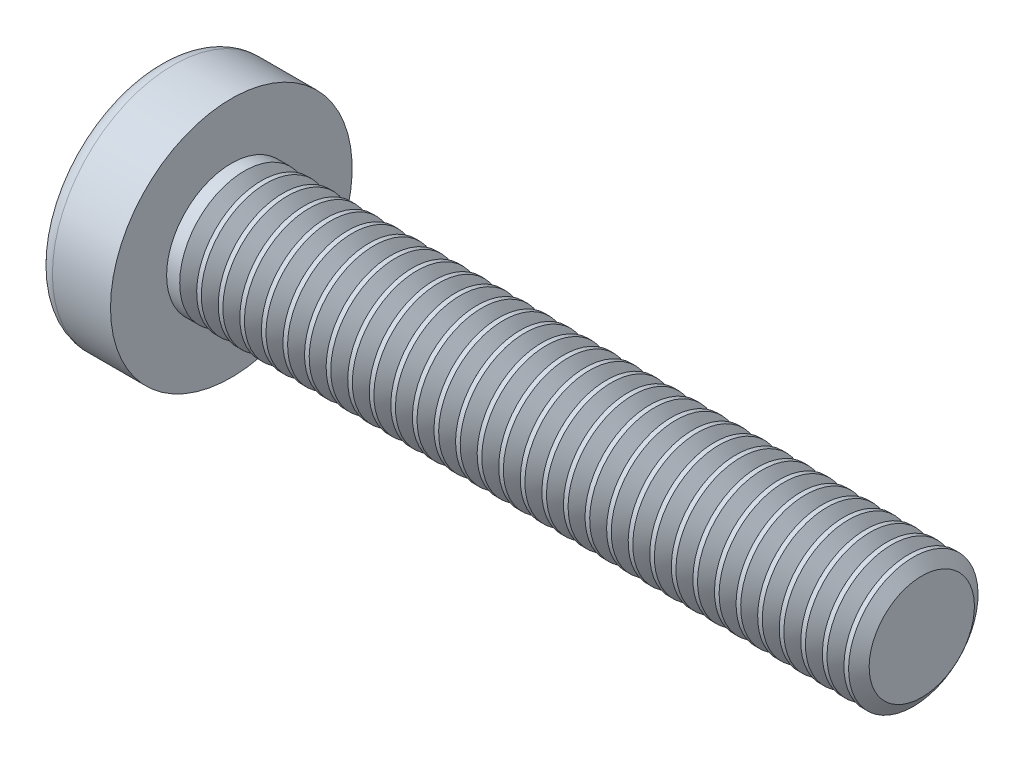
SolidWorks part; units mm, degrees
ref_plane "Plane1" through (0, 0, 0) normal (0, 0, 1) x (1, 0, 0)
ref_plane "Plane2" through (0, 0, 0) normal (0, 1, 0) x (1, 0, 0)
ref_plane "Plane3" through (0, 0, 0) normal (1, 0, 0) x (0, 0, -1)
sketch "BodySke" plane through (0, 0, 0) normal (0, 0, 1) x (1, 0, 0)
  line L0 (2.4, 1.5) -> (2.4, 2.8)
  line L1 (2.9, 6.35) -> (2.9, -3.175) construction
  line L2 (-25.4, 0) -> (127, 0) construction
  line L3 (18.4, 0) -> (0, 0)
  line L4 (2.4, 1.5) -> (18.4, 1.5)
  line L5 (18.4, 1.5) -> (18.4, 0)
  line L6 (1.0534, 2.8) -> (2.4, 2.8)
  line L7 (2.4, -1.5) -> (18.4, -1.5) construction
  line L8 (2.4, 6.35) -> (2.4, -3.175) construction
  arc A0 (0.7472, 2.6293) -> (0, 0) centre (5, 0) ccw
  arc A2 (0.7472, 2.6293) -> (1.0534, 2.8) centre (1.0534, 2.44) cw
  dimension "Head_crown_rad" = 5
  dimension "Head_fillet_rad" = 0.36
  dimension "Diameter" = 3
  dimension "Head_ht" = 2.4
  dimension "Head_dia" = 5.6
  dimension "Advance" = 0.5
revolve "Base-Revolve" add sketch "BodySke" angle 360 about L2
cosmetic thread "ThreadCosmetic" [suppressed] parameters "Thread_length"=15.5, "Thread_minor"=2.439
sketch "Sketch3" plane through (0, 0, 0) normal (1, 0, 0) x (0, 0, -1)
  line L0 (0.37, -1.45) -> (-0.37, -1.45)
  line L1 (0.37, -1.45) -> (0.37, 1.45)
  line L2 (-0.37, 1.45) -> (0.37, 1.45)
  line L3 (-0.37, 1.45) -> (-0.37, -1.45)
  dimension "Cross_dia" = 2.9
  dimension "D1" = 1.45
  dimension "Cross_width" = 0.74
  dimension "D2" = 0.37
ref_plane "Plane4" through (1.76, 0, 0) normal (1, 0, 0) x (0, 0, -1)
sketch "Sketch4" plane through (1.76, 0, 0) normal (1, 0, 0) x (0, 0, -1)
  line L0 (0.185, -0.185) -> (-0.185, -0.185)
  line L1 (0.185, -0.185) -> (0.185, 0.185)
  line L2 (-0.185, 0.185) -> (0.185, 0.185)
  line L3 (-0.185, 0.185) -> (-0.185, -0.185)
  dimension "D2" = 0.37
  dimension "D1" = 0.37
  dimension "D3" = 0.185
  dimension "D4" = 0.185
loft "Cut-Loft1" cut profiles "Sketch3", "Sketch4"
pattern_circular "CirPattern1" count 2 every 90 about axis through (0, 0, 0) along (1, 0, 0) of "Cut-Loft1"
sketch "ThdSchSke" plane through (0, 0, 0) normal (0, 0, 1) x (1, 0, 0)
  line L0 (2.9, -1.2195) -> (2.7036, -1.5)
  line L1 (2.9, -1.2195) -> (3.0964, -1.5)
  line L2 (3.0964, -1.5) -> (3.0964, -1.875)
  line L3 (-3.175, 0) -> (5.1513, 0) construction
  line L5 (3.0964, -1.875) -> (2.7036, -1.875)
  line L6 (2.7036, -1.875) -> (2.7036, -1.5)
  dimension "Diameter" = 3
  dimension "SideAngle" = 55
  dimension "VeeAngle" = 70
  dimension "Thread_minor" = 2.439
  dimension "Overcut" = 3.75
  dimension "Start" = 2.9
revolve "ThreadSchematic" cut sketch "ThdSchSke" angle 360 about L3
pattern_linear "ThdSchPat" count 32 spacing 0.5 along (1, 0, 0) of "ThreadSchematic"
equation "\"D1@Sketch3\" = \"Cross_dia@Sketch3\" / 2"
equation "\"D2@Sketch3\" = \"Cross_width@Sketch3\" / 2"
equation "\"D1@Sketch4\" = \"Cross_width@Sketch3\" *.5"
equation "\"D2@Sketch4\" = \"D1@Sketch4\""
equation "\"D3@Sketch4\" = \"D1@Sketch4\" / 2"
equation "\"D4@Sketch4\" = \"D2@Sketch4\" / 2"
equation "\"Thread_length@ThreadCosmetic\" = ((sgn( (\"Length@BodySke\" - \"Advance@BodySke\" ) - \"Thread_nom@BodySke\" )-1)*( (\"Length@BodySke\" - \"Advance@BodySke\" ) - \"Thread_nom@BodySke\" ))/-2+ \"Thread_nom@BodySke\""
equation "\"Thread_minor@ThdSchSke\" = \"Thread_minor@ThreadCosmetic\""
equation "\"Diameter@ThdSchSke\" = \"Diameter@BodySke\""
equation "\"Overcut@ThdSchSke\" = \"Diameter@BodySke\" * 1.25"
equation "\"Start@ThdSchSke\" = \"Head_ht@BodySke\" + \"Length@BodySke\" - \"Thread_length@ThreadCosmetic\"  '---Non-countersunk---"
equation "\"Num_threads@ThdSchPat\" = int( \"Thread_length@ThreadCosmetic\" / \"Advance@BodySke\" + 0.999 )  + 1"
equation "\"Advance@ThdSchPat\" = \"Thread_length@ThreadCosmetic\" /  (\"Num_threads@ThdSchPat\" - 1) 'relax it"
